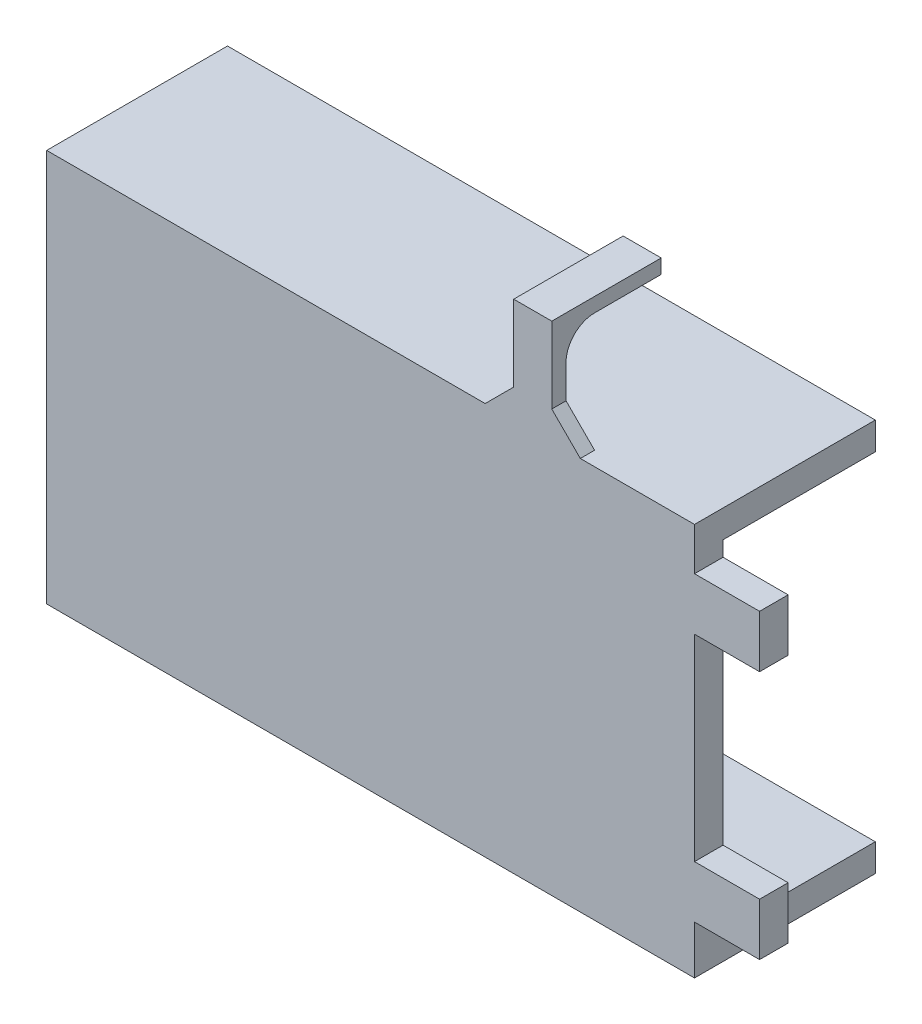
SolidWorks part; units mm, degrees
ref_plane "前视基准面" through (0, 0, 0) normal (0, 0, 1) x (1, 0, 0)
ref_plane "上视基准面" through (0, 0, 0) normal (0, 1, 0) x (1, 0, 0)
ref_plane "右视基准面" through (0, 0, 0) normal (1, 0, 0) x (0, 0, -1)
other "Configuration Table"
sketch "草图1" plane through (0, 0, 0) normal (0, 0, 1) x (1, 0, 0)
  line L1 (16.0353, 26.5433) -> (-52.0424, 26.5433)
  line L2 (16.0353, 26.5433) -> (16.0353, -14.7373)
  line L3 (16.0353, -14.7373) -> (-52.0424, -14.7373)
  line L4 (-52.0424, 26.5433) -> (-52.0424, -14.7373)
  line L5 (13.1353, 23.6433) -> (-49.5424, 23.6433)
  line L6 (13.1353, 23.6433) -> (13.1353, -11.8373)
  line L7 (13.1353, -11.8373) -> (-49.5424, -11.8373)
  line L8 (-49.5424, 23.6433) -> (-49.5424, -11.8373)
extrude "凸台-拉伸1" add sketch "草图1" along normal blind 16
sketch "草图2" plane through (-52.0424, 0, 0) normal (-1, 0, 0) x (0, 0, 1)
  line L0 (0, 26.5433) -> (0, -14.7373) construction
  line L1 (0, 1.2627) -> (7, 1.2627)
  line L2 (0, 1.2627) -> (0, -11.7373)
  line L3 (0, -11.7373) -> (7, -11.7373)
  line L4 (7, 1.2627) -> (7, -11.7373)
  line L6 (16, -14.7373) -> (0, -14.7373) construction
  dimension "D1" = 7
  dimension "D2" = 13
  dimension "D3" = 3
extrude "切除-拉伸1" cut sketch "草图2" against normal up to surface (2.5 mm away) up to face at (-49.5424, 5.903, 8)
sketch "草图3" plane through (16.0353, 0, 0) normal (1, 0, 0) x (0, 0, -1)
  line L0 (-16, -14.7373) -> (-16, 26.5433) construction
  line L1 (-16, -11.8373) -> (0, -11.8373)
  line L2 (-16, -11.8373) -> (-16, 23.6433)
  line L3 (-16, 23.6433) -> (0, 23.6433)
  line L4 (0, -11.8373) -> (0, 23.6433)
  line L8 (-16, 26.5433) -> (0, 26.5433) construction
  line L9 (-16, -14.7373) -> (0, -14.7373) construction
  line L10 (0, -14.7373) -> (0, 26.5433) construction
  dimension "D1" = 2.9
  dimension "D2" = 2.9
  dimension "D3" = 0
extrude "切除-拉伸2" cut sketch "草图3" against normal up to surface (2.9 mm away) up to face at (13.1353, 5.903, 8)
sketch "草图4" plane through (0, 0, 16) normal (0, 0, 1) x (1, 0, 0)
  line L2 (16.0353, 26.5433) -> (-52.0424, 26.5433)
  line L3 (16.0353, 26.5433) -> (16.0353, -14.7373)
  line L4 (16.0353, -14.7373) -> (-52.0424, -14.7373)
  line L5 (-52.0424, 26.5433) -> (-52.0424, -14.7373)
extrude "凸台-拉伸2" add sketch "草图4" along normal blind 3
sketch "草图5" plane through (16.0353, 0, 0) normal (1, 0, 0) x (0, 0, -1)
  line L0 (-19, -14.7373) -> (-19, 26.5433) construction
  line L1 (-19, -9.646) -> (-16, -9.646)
  line L2 (-19, -9.646) -> (-19, 22.054)
  line L3 (-19, 22.054) -> (-16, 22.054)
  line L4 (-16, -9.646) -> (-16, 22.054)
  line L5 (-16, -11.8373) -> (-16, 23.6433) construction
  line L6 (-11.04, -9.546) -> (-12.64, -9.546) construction
  line L7 (-12.64, 21.954) -> (-11.04, 21.954) construction
  line L9 (-19, -4.146) -> (-16, -4.146)
  line L10 (-19, -4.146) -> (-19, 16.554)
  line L11 (-19, 16.554) -> (-16, 16.554)
  line L12 (-16, -4.146) -> (-16, 16.554)
  line M6 (-19, 26.5433) -> (-19, -14.7373)
  line M10 (-16, -11.8373) -> (-16, 23.6433)
  dimension "D1" = 0.1
  dimension "D2" = 0.1
  dimension "D3" = 5.5
  dimension "D4" = 5.5
extrude "凸台-拉伸3" add sketch "草图5" along normal up to surface (6.8387 mm away) contours L9 L2 L1 M10 | L11 L3 M6 M10
sketch "草图6" plane through (-52.0424, 0, 0) normal (-1, 0, 0) x (0, 0, 1)
  line L0 (0, -11.7373) -> (0, -14.7373) construction
  line L1 (0, -12.7373) -> (8, -12.7373)
  line L2 (0, -12.7373) -> (0, 2.2627)
  line L3 (0, 2.2627) -> (8, 2.2627)
  line L4 (8, -12.7373) -> (8, 2.2627)
  line L5 (0, -11.7373) -> (7, -11.7373) construction
  line L6 (7, 1.2627) -> (0, 1.2627) construction
  line L7 (7, -11.7373) -> (7, 1.2627) construction
  dimension "D1" = 1
  dimension "D2" = 1
  dimension "D3" = 1
extrude "切除-拉伸3" cut sketch "草图6" against normal blind 1
sketch "草图7" plane through (-52.0424, 0, 0) normal (-1, 0, 0) x (0, 0, 1)
  line L0 (0, 26.5433) -> (0, 2.2627) construction
  line L1 (0, 18.5433) -> (1.5, 18.5433)
  line L2 (0, 18.5433) -> (0, 11.5433)
  line L3 (0, 11.5433) -> (1.5, 11.5433)
  line L4 (1.5, 18.5433) -> (1.5, 11.5433)
  line L5 (0, 18.5433) -> (-1.5, 18.5433) construction
  line L6 (-1.5, 11.5433) -> (0, 11.5433) construction
  dimension "D1" = 0
  dimension "D2" = 1.5
extrude "凸台-拉伸4" add sketch "草图7" along normal blind 7
sketch "草图8" plane through (0, 0, 1.5) normal (0, 0, 1) x (1, 0, 0)
  line L0 (-59.0424, 18.5433) -> (-52.0424, 18.5433) construction
  line L1 (-59.0424, 11.5433) -> (-59.0424, 18.5433) construction
  circle A0 centre (-56.5424, 15.0433) radius 1.55
  dimension "D1" = 3.5
  dimension "D3" = 3.1
  dimension "D2" = 2.5
extrude "切除-拉伸6" cut sketch "草图8" against normal through all
sketch "草图9" plane through (0, 26.5433, 0) normal (0, 1, 0) x (1, 0, 0)
  line L0 (16.0353, -19) -> (-52.0424, -19) construction
  line L1 (1.0353, -19) -> (-2.9647, -19)
  line L2 (1.0353, -19) -> (1.0353, -17.5)
  line L3 (1.0353, -17.5) -> (-2.9647, -17.5)
  line L4 (-2.9647, -19) -> (-2.9647, -17.5)
  line L5 (16.0353, -19) -> (16.0353, 0) construction
  dimension "D1" = 15
  dimension "D2" = 4
  dimension "D3" = 1.5
extrude "凸台-拉伸5" add sketch "草图9" along normal blind 11
sketch "草图10" plane through (0, 0, 17.5) normal (0, 0, -1) x (-1, 0, 0)
  line L0 (-1.0353, 37.5433) -> (-1.0353, 26.5433) construction
  line L1 (2.9647, 37.5433) -> (-1.0353, 37.5433)
  line L2 (2.9647, 37.5433) -> (2.9647, 36.0433)
  line L3 (2.9647, 36.0433) -> (-1.0353, 36.0433)
  line L4 (-1.0353, 37.5433) -> (-1.0353, 36.0433)
  dimension "D1" = 1.5
extrude "凸台-拉伸6" add sketch "草图10" along normal blind 10
chamfer "倒角1" distance 3 angle 45 2 edges at (1.0353, 26.5433, 18.25) (-2.9647, 26.5433, 18.25)
fillet "圆角1" radius 3 1 edges at (-0.9647, 36.0433, 17.5)
sketch "草图11" plane through (0, -14.7373, 0) normal (0, -1, 0) x (1, 0, 0)
  line L0 (-52.0424, 0) -> (16.0353, 0) construction
  line L1 (-13.9647, 0) -> (-20.9647, 0)
  line L2 (-13.9647, 0) -> (-13.9647, 1.5)
  line L3 (-13.9647, 1.5) -> (-20.9647, 1.5)
  line L4 (-20.9647, 0) -> (-20.9647, 1.5)
  line L5 (-13.9647, -1.5) -> (-13.9647, 0) construction
  dimension "D1" = 7
  dimension "D2" = 1.5
extrude "凸台-拉伸7" add sketch "草图11" along normal blind 7
sketch "草图12" plane through (0, 0, 1.5) normal (0, 0, 1) x (1, 0, 0)
  line L0 (-13.9647, -21.7373) -> (-20.9647, -21.7373) construction
  line L1 (-13.9647, -21.7373) -> (-13.9647, -14.7373) construction
  circle A0 centre (-17.4647, -19.2373) radius 1.55
  dimension "D1" = 3.1
  dimension "D2" = 2.5
  dimension "D3" = 3.5
extrude "切除-拉伸7" cut sketch "草图12" against normal through all
